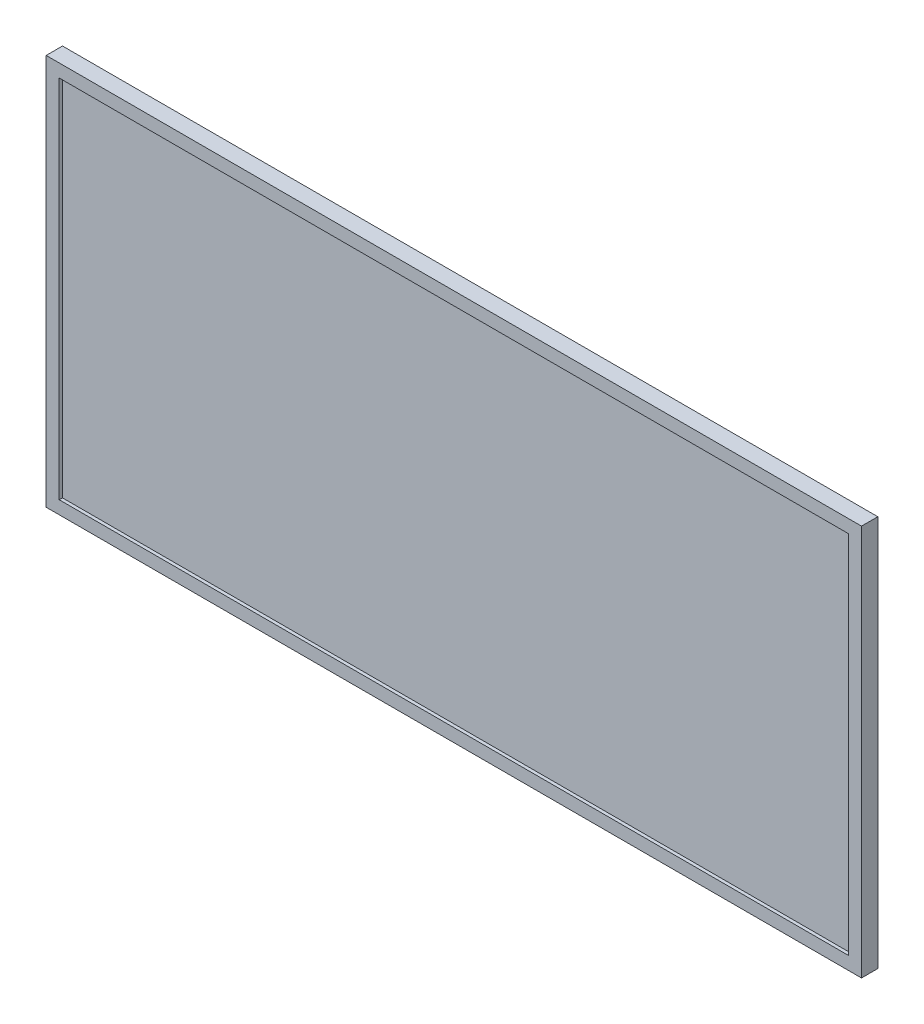
SolidWorks part; units mm, degrees
ref_plane "前基準面" through (0, 0, 0) normal (0, 0, 1) x (1, 0, 0)
ref_plane "上基準面" through (0, 0, 0) normal (0, 1, 0) x (1, 0, 0)
ref_plane "右基準面" through (0, 0, 0) normal (1, 0, 0) x (0, 0, -1)
sketch "草圖1" plane through (0, 0, 0) normal (0, 0, 1) x (1, 0, 0)
  line L1 (250, 120) -> (-250, 120)
  line L2 (250, 120) -> (250, -120)
  line L3 (250, -120) -> (-250, -120)
  line L4 (-250, 120) -> (-250, -120)
  line L5 (250, 120) -> (-250, -120) construction
  line L6 (250, -120) -> (-250, 120) construction
  point P0 (0, 0)
  dimension "D1" = 240
  dimension "D2" = 500
extrude "填料-伸長1" add sketch "草圖1" along normal blind 10
shell "薄殼1" thickness 8
sketch "草圖2" plane through (0, 0, 0) normal (0, 0, -1) x (-1, 0, 0)
  line L1 (-30, -40) -> (30, -40)
  line L2 (-40, -30) -> (-40, 30)
  line L3 (-30, 40) -> (30, 40)
  line L4 (40, -30) -> (40, 30)
  line L5 (-40, -40) -> (40, 40) construction
  line L6 (-40, 40) -> (40, -40) construction
  arc A0 (30, -40) -> (40, -30) centre (30, -30) ccw
  arc A1 (-30, -40) -> (-40, -30) centre (-30, -30) cw
  arc A2 (30, 40) -> (40, 30) centre (30, 30) cw
  arc A3 (-40, 30) -> (-30, 40) centre (-30, 30) cw
  point P0 (0, 0)
  dimension "D3" = 10
  dimension "D1" = 80
  dimension "D2" = 80
extrude "填料-伸長2" add sketch "草圖2" along normal blind 20
sketch "草圖7" plane through (0, 0, -20) normal (0, 0, -1) x (-1, 0, 0)
  circle A1 centre (0, 0) radius 7.25
  dimension "D2" = 14.5
sketch "草圖8" plane through (0, 0, 0) normal (1, 0, 0) x (0, 0, -1)
  line L0 (20, 30) -> (20, -30) construction
  line L1 (20, 30) -> (20, -30)
  line L2 (41.6264, 0) -> (20, 0) construction
  line L3 (20, 3.4) -> (20, -3.4)
  line L4 (20.5, -3.9) -> (20.8, -3.9)
  line L5 (20.8, -3.9) -> (20.8, -6.7235)
  line L6 (21.5069, -7.1787) -> (26.0069, -5.1332)
  line L7 (26.3, -4.678) -> (26.3, 4.678)
  line L8 (21.5069, 7.1787) -> (26.0069, 5.1332)
  line L9 (20.8, 3.9) -> (20.8, 6.7235)
  line L10 (20.5, 3.9) -> (20.8, 3.9)
  line L11 (21.5069, -7.1787) -> (20.7033, -7.5439)
  line L12 (20.8, -6.7235) -> (20.8, -7.5)
  line L13 (52.8742, 8.1543) -> (52.8742, -13.4721) construction
  line L14 (49.4742, -13.4721) -> (56.2742, -13.4721)
  line L15 (56.7742, -12.9721) -> (56.7742, -12.6721)
  line L16 (56.7742, -12.6721) -> (59.5977, -12.6721)
  line L17 (60.0529, -11.9652) -> (58.0074, -7.4652)
  line L18 (57.5522, -7.1721) -> (48.1961, -7.1721)
  line L19 (45.6955, -11.9652) -> (47.741, -7.4652)
  line L20 (48.9742, -12.6721) -> (46.1507, -12.6721)
  line L21 (48.9742, -12.9721) -> (48.9742, -12.6721)
  line L22 (20.8, 6.7235) -> (20.8, 7.5)
  line L23 (21.5069, 7.1787) -> (20.7033, 7.5439)
  line L24 (20.5, 3.9) -> (20, 3.9)
  line L25 (20, 3.9) -> (20, 3.4)
  line L26 (20.8, -3.9) -> (20, -3.9)
  line L27 (20, -3.9) -> (20, -3.4)
  line L28 (20, -3.4) -> (19.9848, -3.3938)
  arc A0 (20, -3.4) -> (20.5, -3.9) centre (20.5, -3.4) ccw
  arc A1 (20.5, 3.9) -> (20, 3.4) centre (20.5, 3.4) ccw
  arc A2 (21.5069, 7.1787) -> (20.8, 6.7235) centre (21.3, 6.7235) ccw
  arc A3 (26.0069, 5.1332) -> (26.3, 4.678) centre (25.8, 4.678) cw
  arc A4 (26.0069, -5.1332) -> (26.3, -4.678) centre (25.8, -4.678) ccw
  arc A5 (20.8, -6.7235) -> (21.5069, -7.1787) centre (21.3, -6.7235) ccw
  arc A6 (56.2742, -13.4721) -> (56.7742, -12.9721) centre (56.2742, -12.9721) ccw
  arc A7 (48.9742, -12.9721) -> (49.4742, -13.4721) centre (49.4742, -12.9721) ccw
  arc A8 (45.6955, -11.9652) -> (46.1507, -12.6721) centre (46.1507, -12.1721) ccw
  arc A9 (47.741, -7.4652) -> (48.1961, -7.1721) centre (48.1961, -7.6721) cw
  arc A10 (58.0074, -7.4652) -> (57.5522, -7.1721) centre (57.5522, -7.6721) ccw
  arc A11 (59.5977, -12.6721) -> (60.0529, -11.9652) centre (59.5977, -12.1721) ccw
  point P10 (26.3, 0)
  point P25 (20, 0)
  point P36 (52.8742, -7.1721)
  dimension "D2" = 0.5
  dimension "D5" = 0.5
  dimension "D1" = 6.3
  dimension "D3" = 5.5
  dimension "D4" = 6.3
  dimension "D6" = 15
  dimension "D7" = 7.8
  dimension "D8" = 9.3561
extrude "填料-伸長3" [suppressed] add sketch "草圖8" along normal mid plane 14 contours L5 A5 L6 A4 L7 A3 L8 A2 L9 L10 A1 L1 A0 L4 | A1 L24 L1 | A0 L1 L26
sketch "草圖9" plane through (0, 0, -20) normal (0, 0, -1) x (-1, 0, 0)
  circle A0 centre (0, 0) radius 1.65
  dimension "D1" = 3.3
extrude "除料-伸長1" cut sketch "草圖9" against normal blind 10
